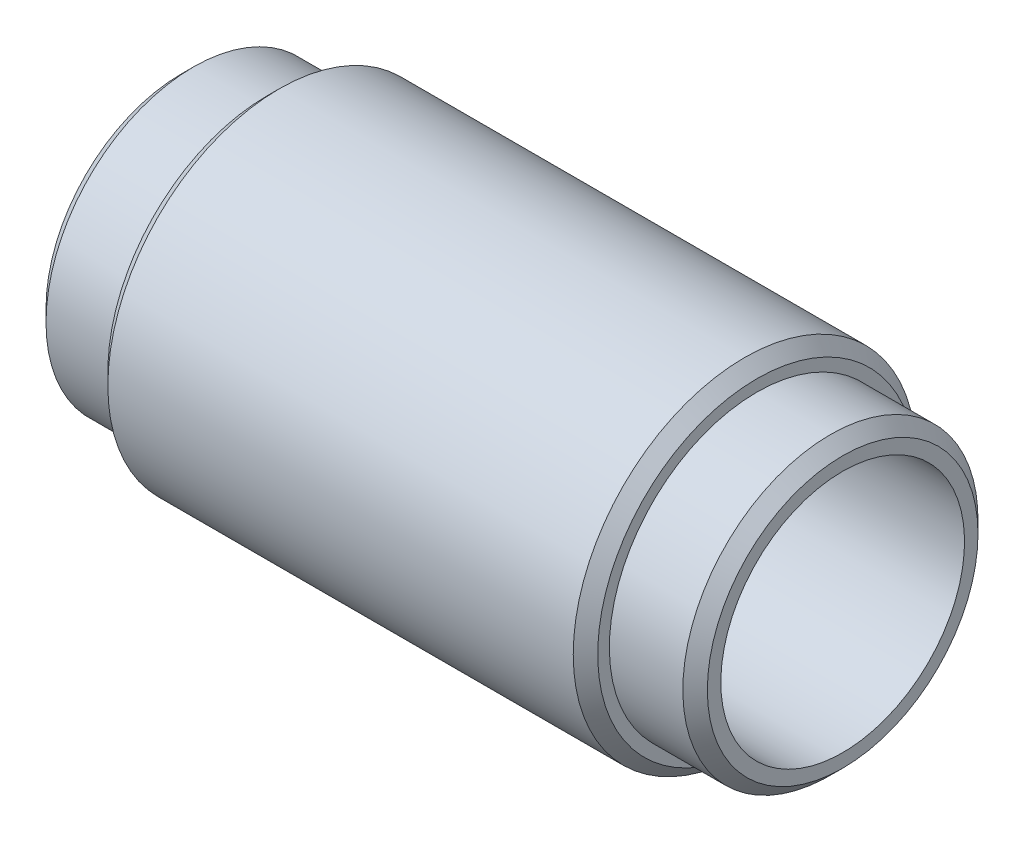
SolidWorks part; units mm, degrees
ref_plane "前视基准面" through (0, 0, 0) normal (0, 0, 1) x (1, 0, 0)
ref_plane "上视基准面" through (0, 0, 0) normal (0, 1, 0) x (1, 0, 0)
ref_plane "右视基准面" through (0, 0, 0) normal (1, 0, 0) x (0, 0, -1)
sketch "草图1" plane through (0, 0, 0) normal (0, 0, 1) x (1, 0, 0)
  line L0 (13.5, 0) -> (-13.5, 0) construction
  line L1 (-13.5, 4.975) -> (13.5, 4.975)
  line L2 (13.5, 4.975) -> (13.5, 6.025)
  line L3 (-10, 6.025) -> (-10, 7)
  line L4 (13.5, 6.025) -> (10, 6.025)
  line L5 (10, 6.025) -> (10, 7)
  line L6 (10, 7) -> (-10, 7)
  line L7 (-13.5, 4.975) -> (-13.5, 6.025)
  line L8 (-13.5, 6.025) -> (-10, 6.025)
  point P4 (0, 0)
  dimension "D1" = 9.95
  dimension "D2" = 12.05
  dimension "D3" = 3.5
  dimension "D4" = 14
  dimension "D5" = 20
revolve "旋转1" add sketch "草图1" angle 360 about L0
chamfer "倒角1" distance 0.5 angle 45 4 edges at (13.5, 6.025, 0) (10, 7, 0) (-13.5, 6.025, 0) (-10, 7, 0)
